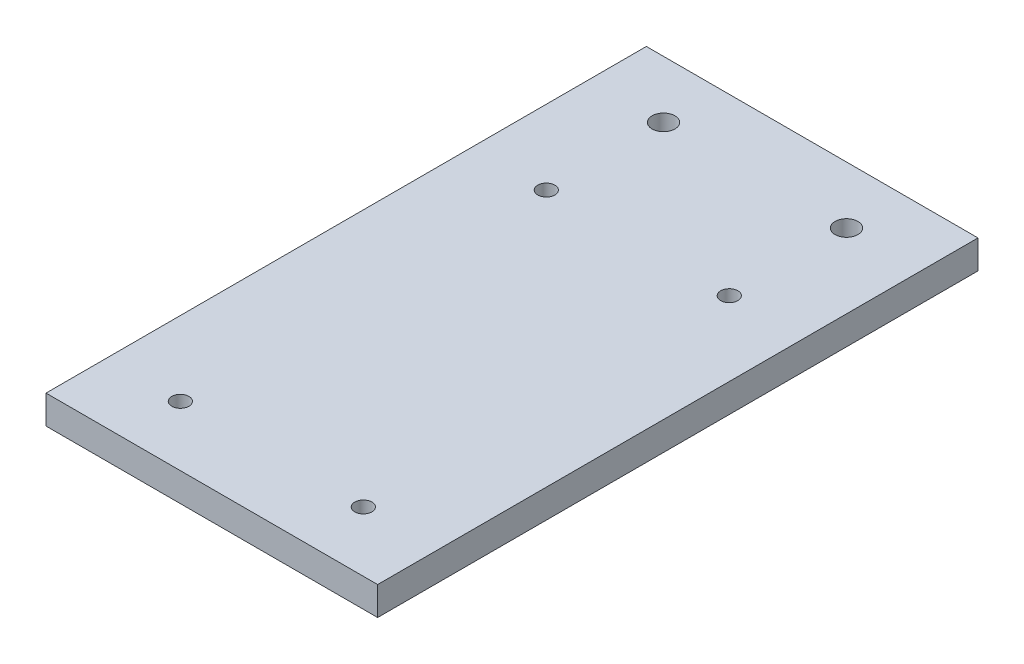
SolidWorks part; units mm, degrees
ref_plane "前视基准面" through (0, 0, 0) normal (0, 0, 1) x (1, 0, 0)
ref_plane "上视基准面" through (0, 0, 0) normal (0, 1, 0) x (1, 0, 0)
ref_plane "右视基准面" through (0, 0, 0) normal (1, 0, 0) x (0, 0, -1)
sketch "Sketch1" plane through (0, 0, 0) normal (0, 1, 0) x (1, 0, 0)
  line L0 (-29, 32.5) -> (29, 32.5) construction
  line L1 (-29, -52.5) -> (29, -52.5)
  line L2 (-29, -52.5) -> (-29, 52.5)
  line L3 (-29, 52.5) -> (29, 52.5)
  line L4 (29, -52.5) -> (29, 52.5)
  line L5 (-29, -52.5) -> (29, 52.5) construction
  line L6 (-29, 52.5) -> (29, -52.5) construction
  line L7 (0, 32.5) -> (0, -52.5) construction
  line L8 (0, -10) -> (29, -10) construction
  line L9 (-16, -42) -> (16, -42) construction
  line L10 (-16, -42) -> (-16, 22) construction
  line L11 (-16, 22) -> (16, 22) construction
  line L12 (16, -42) -> (16, 22) construction
  line L13 (-16, -42) -> (16, 22) construction
  line L14 (-16, 22) -> (16, -42) construction
  line L15 (-16, -42) -> (16, -42) construction
  line L16 (29, 32.5) -> (29, 52.5) construction
  line L17 (29, 42.5) -> (-29, 42.5) construction
  line L18 (-16, 42.5) -> (-16, 22) construction
  line L19 (16, 42.5) -> (16, 22) construction
  circle A0 centre (-16, 22) radius 1.5
  circle A1 centre (16, 22) radius 1.5
  circle A2 centre (16, -42) radius 1.5
  circle A3 centre (-16, -42) radius 1.5
  circle A4 centre (-16, 42.5) radius 2
  circle A5 centre (16, 42.5) radius 2
  point P0 (0, 0)
  point P10 (0, -10)
  dimension "D6" = 3
  dimension "D7" = 4
  dimension "D8" = 4
  dimension "D1" = 105
  dimension "D2" = 58
  dimension "D3" = 20
  dimension "D4" = 64
  dimension "D5" = 32
extrude "Boss-Extrude1" add sketch "Sketch1" along normal blind 5
